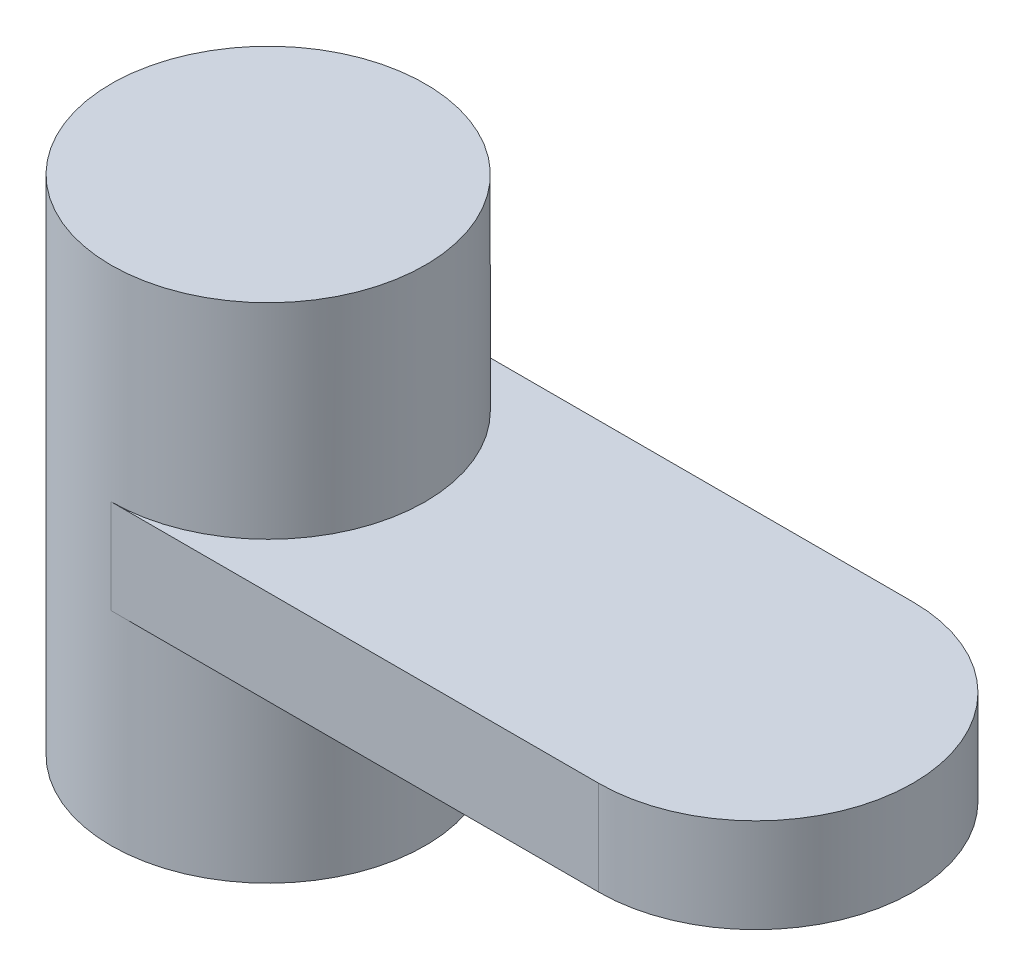
SolidWorks part; units mm, degrees
ref_plane "Front Plane" through (0, 0, 0) normal (0, 0, 1) x (1, 0, 0)
ref_plane "Top Plane" through (0, 0, 0) normal (0, 1, 0) x (1, 0, 0)
ref_plane "Right Plane" through (0, 0, 0) normal (1, 0, 0) x (0, 0, -1)
sketch "Sketch1" plane through (0, 0, 0) normal (0, 1, 0) x (1, 0, 0)
  line L1 (-49.276, 31.75) -> (49.276, 31.75)
  line L3 (-49.276, -31.75) -> (49.276, -31.75)
  arc A0 (-49.276, 31.75) -> (-49.276, -31.75) centre (-49.276, 0) ccw
  arc A1 (49.276, -31.75) -> (49.276, 31.75) centre (49.276, 0) ccw
  point P0 (0, 0)
  dimension "D1" = 98.552
  dimension "D2" = 63.5
extrude "Boss-Extrude1" add sketch "Sketch1" along normal blind 19.05
sketch "Sketch3" plane through (0, 19.05, 0) normal (0, 1, 0) x (1, 0, 0)
  line L0 (-49.276, 31.75) -> (-49.276, -31.75) construction
  circle A0 centre (-49.276, 0) radius 31.75
extrude "Boss-Extrude2" add sketch "Sketch3" along normal blind 41.402 and the other way blind 60.198
